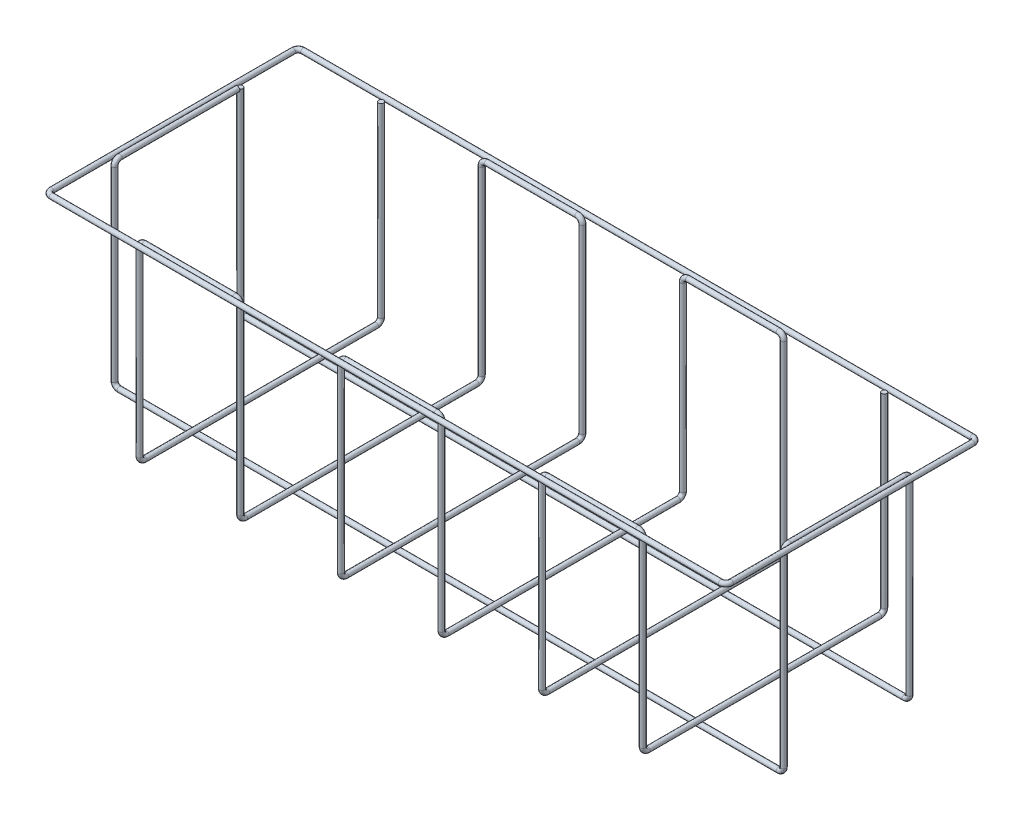
SolidWorks part; units mm, degrees
ref_plane "Front Plane" through (0, 0, 0) normal (0, 0, 1) x (1, 0, 0)
ref_plane "Top Plane" through (0, 0, 0) normal (0, 1, 0) x (1, 0, 0)
ref_plane "Right Plane" through (0, 0, 0) normal (1, 0, 0) x (0, 0, -1)
sketch "Sketch3" plane through (0, 0, 0) normal (0, 1, 0) x (1, 0, 0)
  line L1 (332.5, -125) -> (-332.5, -125)
  line L2 (337.5, -120) -> (337.5, 120)
  line L3 (332.5, 125) -> (-332.5, 125)
  line L4 (-337.5, -120) -> (-337.5, 120)
  line L5 (337.5, -125) -> (-337.5, 125) construction
  line L6 (337.5, 125) -> (-337.5, -125) construction
  arc A0 (-332.5, -125) -> (-337.5, -120) centre (-332.5, -120) cw
  arc A1 (-332.5, 125) -> (-337.5, 120) centre (-332.5, 120) ccw
  arc A2 (332.5, -125) -> (337.5, -120) centre (332.5, -120) ccw
  arc A3 (337.5, 120) -> (332.5, 125) centre (332.5, 120) ccw
  point P0 (0, 0)
  point P18 (-337.5, 62.5)
  point P19 (-332.5, 62.5)
  point P20 (-250.1, 120)
  dimension "D3" = 5
  dimension "D1" = 675
  dimension "D2" = 250
  dimension "D4" = 62.5
  dimension "D5" = 5
  dimension "D6" = 5
  dimension "D7" = 87.4
sketch "Sketch4" plane through (0, 0, 0) normal (1, 0, 0) x (0, 0, -1)
  line L0 (125, 0) -> (-125, 0) construction
  circle A0 centre (-125, 0) radius 2.5
  dimension "D1" = 5
sweep "Sweep2" add profiles "Sketch4" path "Sketch3"
sketch3d "3DSketch6"
  line L0 (-332.5, 0, -62.5) -> (-332.5, -190, -62.5)
  line L1 (-327.5, -195, -62.5) -> (327.5, -195, -62.5)
  line L2 (332.5, -190, -62.5) -> (332.5, -5, -62.5)
  line L3 (332.5, 0, -57.5) -> (332.5, 0, 57.5)
  line L4 (332.5, -5, 62.5) -> (332.5, -190, 62.5)
  line L5 (327.5, -195, 62.5) -> (-327.5, -195, 62.5)
  line L6 (-332.5, -190, 62.5) -> (-332.5, -5, 62.5)
  line L7 (-332.5, 0, 57.5) -> (-332.5, 0, -59.5)
  arc A0 (-332.5, -190, -62.5) -> (-327.5, -195, -62.5) centre (-327.5, -190, -62.5) ccw
  arc A1 (-327.5, -195, 62.5) -> (-332.5, -190, 62.5) centre (-327.5, -190, 62.5) ccw
  arc A2 (-332.5, -5, 62.5) -> (-332.5, 0, 57.5) centre (-332.5, -5, 57.5) ccw
  arc A3 (332.5, -190, 62.5) -> (327.5, -195, 62.5) centre (327.5, -190, 62.5) ccw
  arc A4 (327.5, -195, -62.5) -> (332.5, -190, -62.5) centre (327.5, -190, -62.5) ccw
  arc A5 (332.5, -5, -62.5) -> (332.5, 0, -57.5) centre (332.5, -5, -57.5) ccw
  arc A6 (332.5, 0, 57.5) -> (332.5, -5, 62.5) centre (332.5, -5, 57.5) ccw
  point P12 (-332.5, -195, -62.5)
  point P13 (-327.5, -190, -57.5)
  point P16 (-332.5, -195, 62.5)
  point P17 (-327.5, -190, 57.5)
  point P20 (-332.5, 0, 62.5)
  point P21 (-337.5, -5, 57.5)
  point P24 (332.5, -195, 62.5)
  point P25 (327.5, -190, 57.5)
  point P28 (332.5, -195, -62.5)
  point P29 (327.5, -190, -57.5)
  point P32 (332.5, 0, -62.5)
  point P33 (337.5, -5, -57.5)
  point P36 (332.5, 0, 62.5)
  point P37 (337.5, -5, 57.5)
  dimension "D9" = 5
  dimension "D10" = 5
  dimension "D1" = 195
  dimension "D2" = 195
  dimension "D3" = 665
  dimension "D4" = 125
  dimension "D5" = 195
  dimension "D6" = 665
  dimension "D7" = 195
  dimension "D8" = 122
sketch "Sketch14" plane through (0, 0, 0) normal (0, 1, 0) x (1, 0, 0)
  circle A0 centre (-332.5, 62.5) radius 2.5
  dimension "D1" = 5
sweep "Sweep9" add profiles "Sketch14" path "3DSketch6"
sketch3d "3DSketch7"
  line L0 (-250.1, 0, -120) -> (-250.1, -185, -120)
  line L1 (-250.1, -190, -115) -> (-250.1, -190, 115)
  line L2 (-250.1, -185, 120) -> (-250.1, -5, 120)
  line L3 (-245.1, 0, 120) -> (-155.1, 0, 120)
  line L4 (-150.1, -5, 120) -> (-150.1, -185, 120)
  line L5 (-150.1, -190, 115) -> (-150.1, -190, -115)
  line L6 (-150.1, -185, -120) -> (-150.1, -5, -120)
  line L7 (-145.1, 0, -120) -> (-55.1, 0, -120)
  line L8 (-50.1, -5, -120) -> (-50.1, -185, -120)
  line L9 (-50.1, -190, -115) -> (-50.1, -190, 115)
  line L10 (-50.1, -185, 120) -> (-50.1, -5, 120)
  line L11 (-45.1, 0, 120) -> (44.9, 0, 120)
  line L12 (49.9, -5, 120) -> (49.9, -185, 120)
  line L13 (49.9, -190, 115) -> (49.9, -190, -115)
  line L14 (49.9, -185, -120) -> (49.9, -5, -120)
  line L15 (54.9, 0, -120) -> (144.9, 0, -120)
  line L16 (149.9, -5, -120) -> (149.9, -185, -120)
  line L17 (149.9, -190, -115) -> (149.9, -190, 115)
  line L18 (149.9, -185, 120) -> (149.9, -5, 120)
  line L20 (154.9, 0, 120) -> (244.9, 0, 120)
  line L21 (249.9, -5, 120) -> (249.9, -185, 120)
  line L22 (249.9, -190, 115) -> (249.9, -190, -115)
  line L23 (249.9, -185, -120) -> (249.9, 0, -120)
  arc A0 (-250.1, -185, -120) -> (-250.1, -190, -115) centre (-250.1, -185, -115) ccw
  arc A1 (-250.1, -190, 115) -> (-250.1, -185, 120) centre (-250.1, -185, 115) ccw
  arc A2 (-250.1, -5, 120) -> (-245.1, 0, 120) centre (-245.1, -5, 120) ccw
  arc A3 (-155.1, 0, 120) -> (-150.1, -5, 120) centre (-155.1, -5, 120) ccw
  arc A4 (-150.1, -185, 120) -> (-150.1, -190, 115) centre (-150.1, -185, 115) ccw
  arc A5 (-150.1, -190, -115) -> (-150.1, -185, -120) centre (-150.1, -185, -115) ccw
  arc A6 (-150.1, -5, -120) -> (-145.1, 0, -120) centre (-145.1, -5, -120) ccw
  arc A7 (-55.1, 0, -120) -> (-50.1, -5, -120) centre (-55.1, -5, -120) ccw
  arc A8 (-50.1, -185, -120) -> (-50.1, -190, -115) centre (-50.1, -185, -115) ccw
  arc A9 (-50.1, -190, 115) -> (-50.1, -185, 120) centre (-50.1, -185, 115) ccw
  arc A10 (-50.1, -5, 120) -> (-45.1, 0, 120) centre (-45.1, -5, 120) ccw
  arc A11 (44.9, 0, 120) -> (49.9, -5, 120) centre (44.9, -5, 120) ccw
  arc A12 (49.9, -185, 120) -> (49.9, -190, 115) centre (49.9, -185, 115) ccw
  arc A13 (49.9, -190, -115) -> (49.9, -185, -120) centre (49.9, -185, -115) ccw
  arc A14 (49.9, -5, -120) -> (54.9, 0, -120) centre (54.9, -5, -120) ccw
  arc A15 (144.9, 0, -120) -> (149.9, -5, -120) centre (144.9, -5, -120) ccw
  arc A16 (149.9, -185, -120) -> (149.9, -190, -115) centre (149.9, -185, -115) ccw
  arc A17 (149.9, -190, 115) -> (149.9, -185, 120) centre (149.9, -185, 115) ccw
  arc A18 (149.9, -5, 120) -> (154.9, 0, 120) centre (154.9, -5, 120) ccw
  arc A19 (244.9, 0, 120) -> (249.9, -5, 120) centre (244.9, -5, 120) ccw
  arc A20 (249.9, -185, 120) -> (249.9, -190, 115) centre (249.9, -185, 115) ccw
  arc A21 (249.9, -190, -115) -> (249.9, -185, -120) centre (249.9, -185, -115) ccw
  point P27 (-250.1, -190, -120)
  point P28 (-255.1, -185, -115)
  point P31 (-250.1, -190, 120)
  point P32 (-255.1, -185, 115)
  point P35 (-250.1, 0, 120)
  point P36 (-245.1, -5, 115)
  point P39 (-150.1, 0, 120)
  point P40 (-155.1, -5, 115)
  point P43 (-150.1, -190, 120)
  point P44 (-145.1, -185, 115)
  point P47 (-150.1, -190, -120)
  point P48 (-145.1, -185, -115)
  point P51 (-150.1, 0, -120)
  point P52 (-145.1, -5, -125)
  point P55 (-50.1, 0, -120)
  point P56 (-55.1, -5, -125)
  point P59 (-50.1, -190, -120)
  point P60 (-55.1, -185, -115)
  point P63 (-50.1, -190, 120)
  point P64 (-55.1, -185, 115)
  point P67 (-50.1, 0, 120)
  point P68 (-45.1, -5, 115)
  point P71 (49.9, 0, 120)
  point P72 (44.9, -5, 115)
  point P75 (49.9, -190, 120)
  point P76 (54.9, -185, 115)
  point P79 (49.9, -190, -120)
  point P80 (54.9, -185, -115)
  point P83 (49.9, 0, -120)
  point P84 (54.9, -5, -125)
  point P87 (149.9, 0, -120)
  point P88 (144.9, -5, -125)
  point P91 (149.9, -190, -120)
  point P92 (144.9, -185, -115)
  point P95 (149.9, -190, 120)
  point P96 (144.9, -185, 115)
  point P99 (149.9, 0, 120)
  point P100 (154.9, -5, 115)
  point P103 (249.9, 0, 120)
  point P104 (244.9, -5, 115)
  point P107 (249.9, -190, 120)
  point P108 (254.9, -185, 115)
  point P111 (249.9, -190, -120)
  point P112 (254.9, -185, -115)
  dimension "D24" = 5
  dimension "D1" = 190
  dimension "D2" = 240
  dimension "D3" = 190
  dimension "D4" = 100
  dimension "D5" = 190
  dimension "D6" = 240
  dimension "D7" = 190
  dimension "D8" = 100
  dimension "D9" = 240
  dimension "D10" = 190
  dimension "D11" = 100
  dimension "D12" = 190
  dimension "D13" = 240
  dimension "D14" = 190
  dimension "D15" = 190
  dimension "D16" = 100
  dimension "D17" = 190
  dimension "D18" = 240
  dimension "D19" = 190
  dimension "D20" = 100
  dimension "D21" = 190
  dimension "D22" = 240
  dimension "D23" = 190
sketch "Sketch15" plane through (0, 0, 0) normal (0, 1, 0) x (1, 0, 0)
  circle A0 centre (-250.1, 120) radius 2.5
  dimension "D1" = 5
sweep "Sweep10" add profiles "Sketch15" path "3DSketch7"
